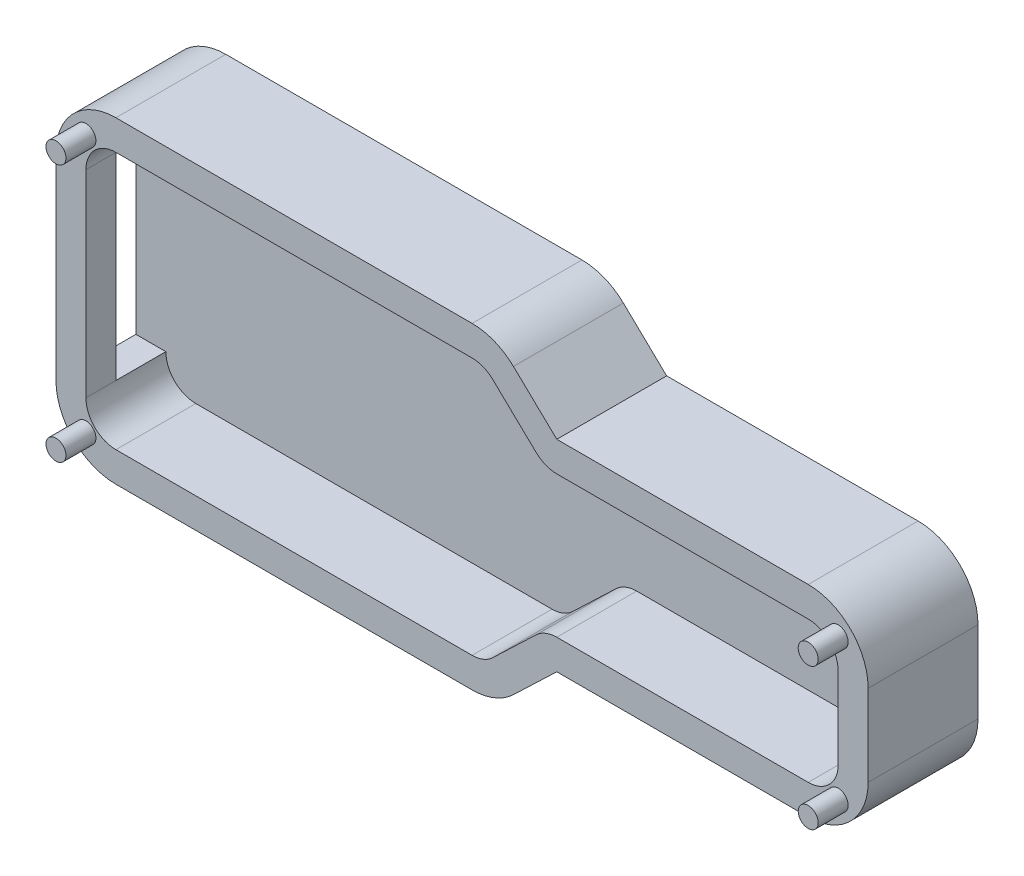
SolidWorks part; units mm, degrees
ref_plane "Front Plane" through (0, 0, 0) normal (0, 0, 1) x (1, 0, 0)
ref_plane "Top Plane" through (0, 0, 0) normal (0, 1, 0) x (1, 0, 0)
ref_plane "Right Plane" through (0, 0, 0) normal (1, 0, 0) x (0, 0, -1)
sketch "Sketch2" plane through (0, 0, 0) normal (0, 0, 1) x (1, 0, 0)
  line L0 (-34.29, 10.16) -> (0, 10.16)
  line L1 (-34.29, 10.16) -> (-34.29, 0)
  line L2 (-34.29, 0) -> (0, 0)
  line L3 (0, 10.16) -> (0, 0)
  line L4 (-69.31, 13.97) -> (-36.29, 13.97)
  line L5 (-69.31, 13.97) -> (-69.31, -3.81)
  line L6 (-69.31, -3.81) -> (-36.29, -3.81)
  line L7 (-36.29, 13.97) -> (-36.29, -3.81)
  line L8 (-31.29, 10.16) -> (-31.29, 0)
  line L9 (-71.31, 15.97) -> (-34.29, 15.97)
  line L10 (-34.29, 15.97) -> (-34.29, 12.16)
  line L11 (-34.29, 12.16) -> (-31.29, 12.16)
  line L12 (-31.29, 12.16) -> (-31.29, -2)
  line L13 (-31.29, -2) -> (-34.29, -2)
  line L14 (-34.29, -2) -> (-34.29, -5.81)
  line L15 (-34.29, -5.81) -> (-71.31, -5.81)
  line L16 (-71.31, -5.81) -> (-71.31, 15.97)
  point P4 (-34.29, 5.08)
  point P5 (-36.29, 5.08)
  dimension "D1" = 2
  dimension "D2" = 2
  dimension "D3" = 2
  dimension "D5" = 2
  dimension "D4" = 2
  dimension "D6" = 0
sketch "Sketch3" plane through (0, 0, 0) normal (0, 0, 1) x (1, 0, 0)
  line L0 (-70.31, 17.97) -> (-34.6529, 17.97)
  line L1 (-32.5796, 17.1383) -> (-28.243, 12.9917)
  line L2 (-26.1697, 12.16) -> (-1, 12.16)
  line L3 (2, 9.16) -> (2, 1)
  line L4 (-1, -2) -> (-26.1697, -2)
  line L5 (-28.243, -2.8317) -> (-32.5796, -6.9783)
  line L6 (-34.6529, -7.81) -> (-70.31, -7.81)
  line L7 (-73.31, -4.81) -> (-73.31, 14.97)
  line L8 (-71.31, 15.97) -> (-34.29, 15.97) construction
  line L9 (-34.29, -5.81) -> (-71.31, -5.81) construction
  line L11 (-34.29, 0) -> (0, 0) construction
  line L12 (0, 10.16) -> (0, 0) construction
  line L13 (-71.31, -5.81) -> (-71.31, 15.97) construction
  line L14 (-70.31, 20.97) -> (-34.6529, 20.97)
  line L15 (-30.5063, 19.3066) -> (-26.1697, 15.16)
  line L16 (-26.1697, 15.16) -> (-1, 15.16)
  line L17 (5, 9.16) -> (5, 1)
  line L18 (-1, -5) -> (-26.1697, -5)
  line L19 (-26.1697, -5) -> (-30.5063, -9.1466)
  line L20 (-34.6529, -10.81) -> (-70.31, -10.81)
  line L21 (-76.31, -4.81) -> (-76.31, 14.97)
  arc A0 (-70.31, -7.81) -> (-73.31, -4.81) centre (-70.31, -4.81) cw
  arc A1 (-1, 12.16) -> (2, 9.16) centre (-1, 9.16) cw
  arc A2 (2, 1) -> (-1, -2) centre (-1, 1) cw
  arc A3 (-32.5796, -6.9783) -> (-34.6529, -7.81) centre (-34.6529, -4.81) cw
  arc A4 (-26.1697, -2) -> (-28.243, -2.8317) centre (-26.1697, -5) ccw
  arc A5 (-28.243, 12.9917) -> (-26.1697, 12.16) centre (-26.1697, 15.16) ccw
  arc A6 (-34.6529, 17.97) -> (-32.5796, 17.1383) centre (-34.6529, 14.97) cw
  arc A7 (-70.31, 17.97) -> (-73.31, 14.97) centre (-70.31, 14.97) ccw
  arc A8 (-34.6529, 20.97) -> (-30.5063, 19.3066) centre (-34.6529, 14.97) cw
  arc A9 (-26.1697, 15.16) -> (-26.1697, 15.16) centre (-26.1697, 15.16) ccw
  arc A10 (-1, 15.16) -> (5, 9.16) centre (-1, 9.16) cw
  arc A11 (5, 1) -> (-1, -5) centre (-1, 1) cw
  arc A12 (-26.1697, -5) -> (-26.1697, -5) centre (-26.1697, -5) ccw
  arc A13 (-30.5063, -9.1466) -> (-34.6529, -10.81) centre (-34.6529, -4.81) cw
  arc A14 (-70.31, -10.81) -> (-76.31, -4.81) centre (-70.31, -4.81) cw
  arc A15 (-70.31, 20.97) -> (-76.31, 14.97) centre (-70.31, 14.97) ccw
  circle A16 centre (-73.31, 17.97) radius 1
  circle A17 centre (-73.31, -7.81) radius 1
  circle A18 centre (2, -2) radius 1
  circle A19 centre (2, 12.16) radius 1
  point P26 (-33.4494, -7.81)
  point P29 (-27.3732, -2)
  point P32 (-27.3732, 12.16)
  point P35 (-33.4494, 17.97)
  dimension "D5" = 3
  dimension "D6" = 2
  dimension "D1" = 2
  dimension "D2" = 2
  dimension "D3" = 2
  dimension "D4" = 2
extrude "Boss-Extrude2" add sketch "Sketch3" along normal blind 8 and the other way blind 3
sketch "Sketch5" plane through (0, 0, -3) normal (0, 0, -1) x (-1, 0, 0)
  line L0 (-2, 1) -> (-2, 9.16) construction
  line L1 (26.1697, -2) -> (1, -2) construction
  line L2 (32.5796, -6.9783) -> (28.243, -2.8317) construction
  line L3 (70.31, -7.81) -> (34.6529, -7.81) construction
  line L4 (73.31, 14.97) -> (73.31, -4.81) construction
  line L5 (-2, 1) -> (-2, 9.16)
  line L6 (26.1697, -2) -> (1, -2)
  line L7 (32.5796, -6.9783) -> (28.243, -2.8317)
  line L8 (73.31, -4.81) -> (73.31, 14.97)
  line L9 (34.6529, -7.81) -> (70.31, -7.81)
  line L10 (28.243, -2.8317) -> (32.5796, -6.9783)
  line L11 (1, -2) -> (26.1697, -2)
  line L12 (-2, 9.16) -> (-2, 1)
  line L13 (26.1697, 12.16) -> (1, 12.16)
  line L14 (32.5796, 17.1383) -> (28.243, 12.9917)
  line L15 (70.31, 17.97) -> (34.6529, 17.97)
  line L16 (73.31, -4.81) -> (73.31, 14.97)
  line L17 (34.6529, -7.81) -> (70.31, -7.81)
  line L18 (28.243, -2.8317) -> (32.5796, -6.9783)
  line L19 (1, -2) -> (26.1697, -2)
  line L20 (-2, 9.16) -> (-2, 1)
  line L21 (26.1697, 12.16) -> (1, 12.16)
  line L22 (32.5796, 17.1383) -> (28.243, 12.9917)
  line L23 (70.31, 17.97) -> (34.6529, 17.97)
  line L24 (70.31, -7.81) -> (34.6529, -7.81)
  line L25 (73.31, 14.97) -> (73.31, -4.81)
  arc A0 (1, 12.16) -> (-2, 9.16) centre (1, 9.16) ccw construction
  arc A1 (-2, 1) -> (1, -2) centre (1, 1) ccw construction
  arc A2 (28.243, -2.8317) -> (26.1697, -2) centre (26.1697, -5) ccw construction
  arc A3 (32.5796, -6.9783) -> (34.6529, -7.81) centre (34.6529, -4.81) ccw construction
  arc A4 (70.31, -7.81) -> (73.31, -4.81) centre (70.31, -4.81) ccw construction
  arc A5 (73.31, 14.97) -> (70.31, 17.97) centre (70.31, 14.97) ccw construction
  arc A6 (1, 12.16) -> (-2, 9.16) centre (1, 9.16) ccw
  arc A7 (-2, 1) -> (1, -2) centre (1, 1) ccw
  arc A8 (70.31, -7.81) -> (73.31, -4.81) centre (70.31, -4.81) ccw
  arc A9 (32.5796, -6.9783) -> (34.6529, -7.81) centre (34.6529, -4.81) ccw
  arc A10 (28.243, -2.8317) -> (26.1697, -2) centre (26.1697, -5) ccw
  arc A11 (-2, 1) -> (1, -2) centre (1, 1) ccw
  arc A12 (1, 12.16) -> (-2, 9.16) centre (1, 9.16) ccw
  arc A13 (26.1697, 12.16) -> (28.243, 12.9917) centre (26.1697, 15.16) ccw
  arc A14 (34.6529, 17.97) -> (32.5796, 17.1383) centre (34.6529, 14.97) ccw
  arc A15 (73.31, 14.97) -> (70.31, 17.97) centre (70.31, 14.97) ccw
  arc A16 (70.31, -7.81) -> (73.31, -4.81) centre (70.31, -4.81) ccw
  arc A17 (32.5796, -6.9783) -> (34.6529, -7.81) centre (34.6529, -4.81) ccw
  arc A18 (28.243, -2.8317) -> (26.1697, -2) centre (26.1697, -5) ccw
  arc A19 (-2, 1) -> (1, -2) centre (1, 1) ccw
  arc A20 (1, 12.16) -> (-2, 9.16) centre (1, 9.16) ccw
  arc A21 (26.1697, 12.16) -> (28.243, 12.9917) centre (26.1697, 15.16) ccw
  arc A22 (34.6529, 17.97) -> (32.5796, 17.1383) centre (34.6529, 14.97) ccw
  arc A23 (73.31, 14.97) -> (70.31, 17.97) centre (70.31, 14.97) ccw
  arc A24 (28.243, -2.8317) -> (26.1697, -2) centre (26.1697, -5) ccw
  arc A25 (32.5796, -6.9783) -> (34.6529, -7.81) centre (34.6529, -4.81) ccw
  arc A26 (70.31, -7.81) -> (73.31, -4.81) centre (70.31, -4.81) ccw
  arc A27 (73.31, 14.97) -> (70.31, 17.97) centre (70.31, 14.97) ccw
  line M17 (73.31, 14.97) -> (73.31, -4.81)
  arc M18 (73.31, -4.81) -> (70.31, -7.81) centre (70.31, -4.81) cw
  line M19 (70.31, -7.81) -> (34.6529, -7.81)
  arc M20 (34.6529, -7.81) -> (32.5796, -6.9783) centre (34.6529, -4.81) cw
  line M21 (32.5796, -6.9783) -> (28.243, -2.8317)
  arc M22 (28.243, -2.8317) -> (26.1697, -2) centre (26.1697, -5) ccw
  line M23 (26.1697, -2) -> (1, -2)
  arc M24 (1, -2) -> (-2, 1) centre (1, 1) cw
  line M25 (-2, 1) -> (-2, 9.16)
  arc M26 (-2, 9.16) -> (1, 12.16) centre (1, 9.16) cw
  line M27 (1, 12.16) -> (26.1697, 12.16)
  arc M28 (26.1697, 12.16) -> (28.243, 12.9917) centre (26.1697, 15.16) ccw
  line M29 (28.243, 12.9917) -> (32.5796, 17.1383)
  arc M30 (32.5796, 17.1383) -> (34.6529, 17.97) centre (34.6529, 14.97) cw
  line M31 (34.6529, 17.97) -> (70.31, 17.97)
  arc M32 (70.31, 17.97) -> (73.31, 14.97) centre (70.31, 14.97) cw
  dimension "D1" = 0
extrude "Boss-Extrude3" add sketch "Sketch5" against normal blind 3 contours M17 M32 M31 M30 M29 M28 M27 M26 M25 M24 M23 M22 M21 M20 M19 M18
sketch "Sketch7" plane through (0, 0, 8) normal (0, 0, 1) x (1, 0, 0)
  circle A0 centre (-73.31, 17.97) radius 1 construction
  circle A1 centre (-73.31, 17.97) radius 1
  circle A2 centre (2, -2) radius 1 construction
  circle A3 centre (2, -2) radius 1
  circle A4 centre (2, 12.16) radius 1 construction
  circle A5 centre (2, 12.16) radius 1
  circle A6 centre (-73.31, -7.81) radius 1 construction
  circle A7 centre (-73.31, -7.81) radius 1
extrude "Boss-Extrude4" add sketch "Sketch7" against normal blind 11 and the other way blind 3
sketch "Sketch9" plane through (-76.31, 0, 0) normal (-1, 0, 0) x (0, 0, 1)
  line L0 (0, 14.97) -> (0, -4.81)
  line L1 (-3, 14.97) -> (8, 14.97) construction
  line L2 (-3, -4.81) -> (8, -4.81) construction
  line L3 (0, -4.81) -> (5, -4.81)
  line L4 (5, -4.81) -> (5, 14.97)
  line L5 (5, 14.97) -> (0, 14.97)
extrude "Cut-Extrude2" cut sketch "Sketch9" against normal blind 10
equation "\"D5@Sketch2\"=\"pcb_overflow\""
equation "\"D1@Sketch2\"=\"pcb_overflow\""
equation "\"D2@Sketch2\"=\"pcb_overflow\""
equation "\"D4@Sketch2\"=\"pcb_overflow\""
equation "\"D3@Sketch2\"=\"pcb_overflow\""
equation "\"D1@Sketch3\"=\"gap_from_case\""
equation "\"D2@Sketch3\"=\"gap_from_case\""
equation "\"D3@Sketch3\"=\"gap_from_case\""
equation "\"D4@Sketch3\"=\"gap_from_case\""
equation "\"D6@Sketch3\"=\"notch_dia\""
